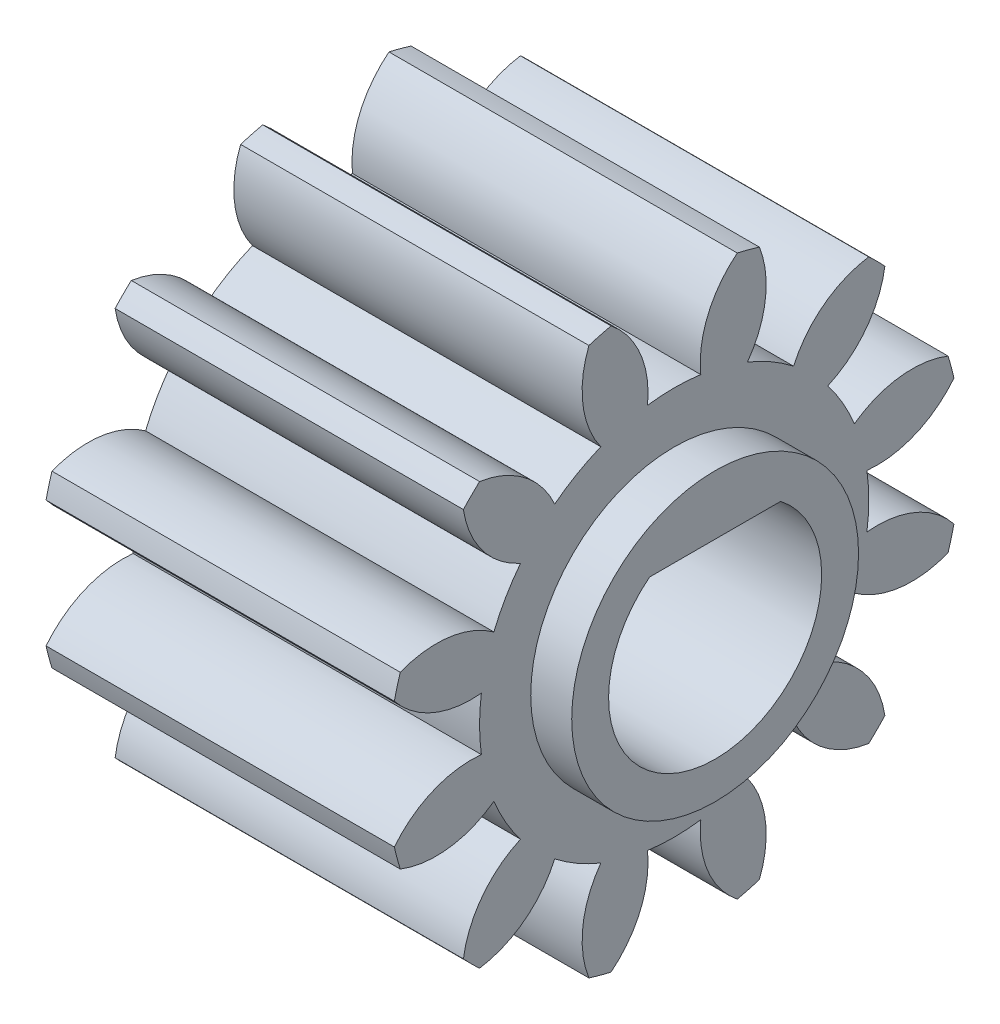
SolidWorks part; units mm, degrees
ref_plane "Plane1" through (0, 0, 0) normal (0, 0, 1) x (1, 0, 0)
ref_plane "Plane2" through (0, 0, 0) normal (0, 1, 0) x (1, 0, 0)
ref_plane "Plane3" through (0, 0, 0) normal (1, 0, 0) x (0, 0, -1)
sketch "HoldingSke" plane through (0, 0, 0) normal (0, 1, 0) x (1, 0, 0)
  line L0 (0, 0) -> (0.9781, -0.2079)
  line L1 (-15, 0) -> (100, 0) construction
  line L2 (0, 0) -> (-2.1039, 2.3779)
  line L3 (0, 0) -> (-11.863, 4.5341)
  line L4 (0, 0) -> (8.4473, 1.7955)
  line L5 (0, 0) -> (-46.8476, -17.4728)
  line L6 (0, 0) -> (-8.2896, -5.593)
  line L7 (-2.1039, 2.3779) -> (8.6586, 51.2059)
  line L8 (-76.2, 54.61) -> (-75.3, 54.61)
  line L9 (-67.7845, 28.3722) -> (-49.3413, 33.142)
  line L10 (-76.2, 71.12) -> (104.1128, 71.12)
  line L11 (0, 0) -> (-10, 0)
  line L12 (-76.2, 101.6) -> (-76.162, 101.6)
  line L13 (24.9733, 27.94) -> (52.9518, 28.4284)
  line L14 (24.9733, 27.94) -> (24.9743, 27.94)
  line L15 (24.9733, 27.94) -> (100.4006, 29.5858)
  line L16 (-63.627, -1) -> (-12.827, -1)
  circle A0 centre (0, 0) radius 2.5
  circle A1 centre (0, 0) radius 4.749
  circle A2 centre (0, 0) radius 37.5
  circle A3 centre (0, 0) radius 2.5
  dimension "MHD" = 9.498
  dimension "Hub_dia" = 75
  dimension "Bore" = 5
  dimension "MBD" = 5
  dimension "Num_teeth" = 12
  dimension "Pitch" = 1
  dimension "Overall_len" = 50
  dimension "Show_teeth" = 12
  dimension "Thickness" = 10
  dimension "OAL" = 50.0001
  dimension "T_dim" = 0.9
  dimension "Ap" = 14.5
  dimension "H" = 19.05
  dimension "Pitch_radius" = 180.3128
  dimension "Width" = 10
  dimension "Backlash" = 0.038
  dimension "Addendum_fac" = 1
  dimension "Dedendum_fac" = 1.25
  dimension "Clearance_fac" = 0.25
  dimension "Dedendum_add" = 0.001
  dimension "Module" = 1
sketch "BasProSke" plane through (0, 0, 0) normal (0, 1, 0) x (1, 0, 0)
  line L0 (-10, 0) -> (60, 0) construction
  line L1 (0, 0) -> (0, 7)
  line L2 (0, 0) -> (8.5, 0)
  line L3 (8.5, 0) -> (8.5, 7)
  line L4 (8.5, 7) -> (0, 7)
  dimension "Thickness" = 8.5
  dimension "Diameter" = 14
revolve "Base-Revolve" add sketch "BasProSke" angle 360 about L0
sketch "TooCutSke" plane through (0, 0, 0) normal (1, 0, 0) x (0, 0, -1)
  line L1 (0, 0) -> (0, 107) construction
  line L2 (0, 0) -> (-0.8496, 5.9395) construction
  line L3 (0, 0) -> (-3.0836, 11.5081) construction
  line L4 (-0.8496, 5.9395) -> (-1.5418, 5.7541) construction
  arc A0 (0.6497, 4.7044) -> (-0.6497, 4.7044) centre (0, 0) ccw
  arc A1 (1.5664, 6.8486) -> (-1.5664, 6.8486) centre (0, 0) ccw
  circle A2 centre (0, 0) radius 6 construction
  circle A3 centre (0, 0) radius 5.8089 construction
  arc A4 (-0.6497, 4.7044) -> (-1.5664, 6.8486) centre (-3.0369, 4.9518) ccw
  arc A5 (1.5664, 6.8486) -> (0.6497, 4.7044) centre (3.0369, 4.9518) ccw
  dimension "Root_dia" = 9.498
  dimension "Overcut_dia" = 14.0508
  dimension "Pitch_dia" = 12
  dimension "Base_dia" = 11.6178
  dimension "Flank_rad" = 2.4
  dimension "Half_ang" = 15
  dimension "Half_CT" = 0.7167
extrude "ToothCut" cut sketch "TooCutSke" along normal through all
fillet "Breaks" [suppressed] radius 0.02
fillet "RootFillets" [suppressed] radius 0.251
pattern_circular "TeethCuts" count 12 every 30 about axis through (-10, 0, 0) along (1, 0, 0) of "ToothCut", "RootFillets", "Breaks"
sketch "HubNeaOneSke" plane through (0, 0, 0) normal (-1, 0, 0) x (0, 0, 1)
  circle A0 centre (0, 0) radius 4.749
  dimension "Diameter" = 9.498
extrude "HubNearOne" [suppressed] add sketch "HubNeaOneSke" along normal blind 41.5001
sketch "HubNeaBotSke" plane through (0, 0, 0) normal (-1, 0, 0) x (0, 0, 1)
  circle A0 centre (0, 0) radius 4.749
  dimension "Diameter" = 9.498
extrude "HubNearBoth" [suppressed] add sketch "HubNeaBotSke" along normal blind 20.75
ref_plane "FarPln" through (8.5, 0, 0) normal (1, 0, 0) x (0, 0, -1)
sketch "HubFarSke" plane through (8.5, 0, 0) normal (1, 0, 0) x (0, 0, -1)
  circle A0 centre (0, 0) radius 4.749
  dimension "Diameter" = 9.498
extrude "HubFar" [suppressed] add sketch "HubFarSke" along normal blind 20.75
sketch "BorSke" plane through (0, 0, 0) normal (1, 0, 0) x (0, 0, -1)
  circle A0 centre (0, 0) radius 2.6
  dimension "Diameter" = 5.2
extrude "Bore" cut sketch "BorSke" along normal mid plane 100.0001
sketch "KeySke" plane through (0, 0, 0) normal (1, 0, 0) x (0, 0, -1)
  line L0 (-1, 0) -> (-1, 3.4)
  line L1 (-1, 3.4) -> (1, 3.4)
  line L2 (1, 3.4) -> (1, 0)
  line L3 (0, 0) -> (0, 34) construction
  line L4 (-1, 0) -> (1, 0)
  dimension "Offset" = 3.4
  dimension "Width" = 2
extrude "Keyway" [suppressed] cut sketch "KeySke" along normal mid plane 100.0001
pattern_circular "Keyway2" [suppressed] count 2 every 90 about axis through (-10, 0, 0) along (1, 0, 0)
sketch "Sketch1" plane through (8.5, 0, 0) normal (1, 0, 0) x (0, 0, -1)
  line L0 (-1.5992, 2.05) -> (1.5992, 2.05)
  circle A0 centre (0, 0) radius 2.6 construction
  arc A1 (1.5992, 2.05) -> (-1.5992, 2.05) centre (0, 0) ccw
  dimension "D1" = 2.05
extrude "Boss-Extrude1" add sketch "Sketch1" against normal up to surface (8.5 mm away) up to face at (0, 0, -2.6)
sketch "Sketch2" plane through (8.5, 0, 0) normal (1, 0, 0) x (0, 0, -1)
  line L0 (-1.5992, 2.05) -> (1.5992, 2.05) construction
  line L1 (-1.5992, 2.05) -> (1.5992, 2.05)
  circle A0 centre (0, 0) radius 3.5
  arc A1 (-1.5992, 2.05) -> (1.5992, 2.05) centre (0, 0) ccw construction
  arc A2 (-1.5992, 2.05) -> (1.5992, 2.05) centre (0, 0) ccw
  dimension "D1" = 7
extrude "Boss-Extrude2" add sketch "Sketch2" along normal blind 1
equation "' \"Module@HoldingSke\" = 6.35"
equation "' \"Num_teeth@HoldingSke\" = 12"
equation "' \"Ap@HoldingSke\" =  20"
equation "' \"Ap@HoldingSke\" = 20"
equation "' \"Width@HoldingSke\" = 0.5 * 25.4"
equation "' \"Hub_dia@HoldingSke\"= 1 * 25.4"
equation "' \"Hub_dia@HoldingSke\" = 1 * 25.4"
equation "' \"Overall_len@HoldingSke\" = 1.0 * 25.4"
equation "' \"Bore@HoldingSke\" = 0.75 * 25.4"
equation "' \"T_dim@HoldingSke\" = 0.1 * 25.4"
equation "' \"Width@KeySke\" = 0.25 * 25.4"
equation "' \"Show_teeth@HoldingSke\" = 13"
equation "' \"Backlash@HoldingSke\" = 0.009 * 25.4"
equation "' \"Addendum_fac@HoldingSke\" = 1.0"
equation "' \"Dedendum_fac@HoldingSke\" = 1.25"
equation "' \"Dedendum_add@HoldingSke\" = 0.00005 * 25.4"
equation "' \"Clearance_fac@HoldingSke\" = 0.25"
equation "\"Pitch@HoldingSke\" = 1 / \"Module@HoldingSke\""
equation "\"Overcut_dia@TooCutSke\" = (\"Num_teeth@HoldingSke\" + 2 * \"Addendum_fac@HoldingSke\") / \"Pitch@HoldingSke\" + 0.002 * 25.4"
equation "\"Pitch_dia@TooCutSke\" = \"Num_teeth@HoldingSke\" / \"Pitch@HoldingSke\""
equation "\"Base_dia@TooCutSke\" = \"Num_teeth@HoldingSke\" / \"Pitch@HoldingSke\" * cos((\"Ap@HoldingSke\"  * 3.14159265 / 180))"
equation "\"Root_dia@TooCutSke\" = (\"Num_teeth@HoldingSke\" + 2) / \"Pitch@HoldingSke\" - 2 * (\"Addendum_fac@HoldingSke\" + \"Dedendum_fac@HoldingSke\") / \"Pitch@HoldingSke\" - \"Dedendum_add@HoldingSke\" * 2"
equation "\"Half_ang@TooCutSke\" = 180 / \"Num_teeth@HoldingSke\""
equation "\"Half_CT@TooCutSke\" = \"Num_teeth@HoldingSke\" / \"Pitch@HoldingSke\" * sin((3.14159265 / 2 / \"Num_teeth@HoldingSke\")) / 2 - 7 * \"Backlash@HoldingSke\" / 4"
equation "\"Flank_rad@TooCutSke\" = \"Num_teeth@HoldingSke\" / \"Pitch@HoldingSke\" / 5"
equation "\"Radius@RootFillets\" = \"Clearance_fac@HoldingSke\" / \"Pitch@HoldingSke\" + \"Dedendum_add@HoldingSke\""
equation "\"Break_rad@Breaks\" = 0.02 / \"Pitch@HoldingSke\""
equation "\"Thickness@HoldingSke\" = \"Width@HoldingSke\""
equation "\"OAL@HoldingSke\" = \"Thickness@HoldingSke\""
equation "\"MHD@HoldingSke\" = (\"Num_teeth@HoldingSke\" + 2) / \"Pitch@HoldingSke\" - 2 * (\"Addendum_fac@HoldingSke\" + \"Dedendum_fac@HoldingSke\")  / \"Pitch@HoldingSke\" - \"Dedendum_add@HoldingSke\" * 2"
equation "\"MBD@HoldingSke\" = (\"Num_teeth@HoldingSke\" + 2) / \"Pitch@HoldingSke\" - 2 * (\"Addendum_fac@HoldingSke\" + \"Dedendum_fac@HoldingSke\")  / \"Pitch@HoldingSke\" - \"Dedendum_add@HoldingSke\" * 2 - 0.002 * 25.4"
equation "\"MHD@HoldingSke\" = ((sgn( \"MHD@HoldingSke\" - \"Hub_dia@HoldingSke\" )-1)*( \"MHD@HoldingSke\" - \"Hub_dia@HoldingSke\" ))/-2+ \"Hub_dia@HoldingSke\""
equation "\"MBD@HoldingSke\" = ((sgn( \"MBD@HoldingSke\" - \"Bore@HoldingSke\" )-1)*( \"MBD@HoldingSke\" - \"Bore@HoldingSke\" ))/-2+ \"Bore@HoldingSke\""
equation "\"OAL@HoldingSke\" = ((sgn( \"OAL@HoldingSke\" - \"Overall_len@HoldingSke\" )+1)*( \"OAL@HoldingSke\" - \"Overall_len@HoldingSke\" ))/2 + \"Overall_len@HoldingSke\" + 0.000002 * 25.4"
equation "\"Num_teeth@TeethCuts\" = int( \"Show_teeth@HoldingSke\" ) + 1"
equation "\"Num_teeth@TeethCuts\" = ((sgn( \"Num_teeth@TeethCuts\" - \"Num_teeth@HoldingSke\" )-1)*( \"Num_teeth@TeethCuts\" - \"Num_teeth@HoldingSke\" ))/-2+ \"Num_teeth@HoldingSke\""
equation "\"Num_teeth@TeethCuts\" = ((sgn( \"Num_teeth@TeethCuts\" - 2.0)+1)*( \"Num_teeth@TeethCuts\" - 2.0))/2 +2.0"
equation "\"Angle@TeethCuts\" = 360.0 / \"Num_teeth@HoldingSke\""
equation "\"Diameter@BasProSke\" = (\"Num_teeth@HoldingSke\" + 2 * \"Addendum_fac@HoldingSke\") / \"Pitch@HoldingSke\""
equation "' \"Fillet_rad@BasProSke\" =  \"Thickness@HoldingSke\" * 0.05"
equation "' \"Fillet_rad@BasProSke\" = \"Thickness@HoldingSke\" * 0.05"
equation "\"MHD@HoldingSke\" = ((sgn( \"MHD@HoldingSke\" - \"Root_dia@TooCutSke\" )-1)*( \"MHD@HoldingSke\" - \"Root_dia@TooCutSke\" ))/-2+ \"Root_dia@TooCutSke\""
equation "\"Diameter@HubNeaOneSke\" = \"MHD@HoldingSke\""
equation "\"Length@HubNearOne\" = \"OAL@HoldingSke\" - \"Thickness@BasProSke\""
equation "\"Diameter@HubNeaBotSke\" = \"MHD@HoldingSke\""
equation "\"Length@HubNearBoth\" = ( \"OAL@HoldingSke\" - \"Thickness@BasProSke\" ) / 2.0"
equation "\"Thickness@FarPln\" = \"Thickness@BasProSke\""
equation "\"Diameter@HubFarSke\" = \"MHD@HoldingSke\""
equation "\"Length@HubFar\" = ( \"OAL@HoldingSke\" - \"Thickness@BasProSke\" ) / 2.0"
equation "\"D1@Bore\" = \"OAL@HoldingSke\" * 2.0"
equation "\"D1@Keyway\" = \"OAL@HoldingSke\" * 2.0"
equation "\"Offset@KeySke\" = \"T_dim@HoldingSke\" + \"MBD@HoldingSke\" / 2.0"
